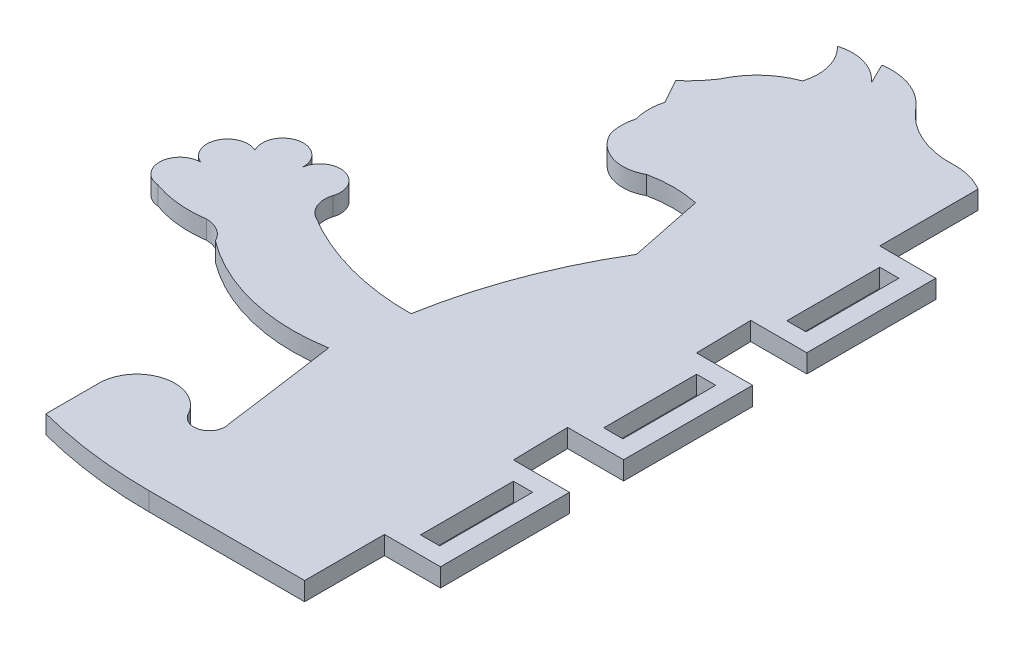
SolidWorks part; units mm, degrees
material "Roble"
ref_plane "Alzado" through (0, 0, 0) normal (0, 0, 1) x (1, 0, 0)
ref_plane "Planta" through (0, 0, 0) normal (0, 1, 0) x (1, 0, 0)
ref_plane "Vista lateral" through (0, 0, 0) normal (1, 0, 0) x (0, 0, -1)
sketch "Croquis1" plane through (0, 0, 0) normal (0, 1, 0) x (1, 0, 0)
  line L0 (0, 0) -> (-25.3533, 0)
  line L5 (0, 0) -> (0, 13)
  line L6 (0, 13) -> (9.123, 13)
  line L7 (9.123, 13) -> (9.123, 34)
  line L8 (9.123, 34) -> (0, 34)
  line L15 (-44.5719, 2.4618) -> (-44.5719, 11.0757)
  line L19 (0, 0) -> (-25.3533, 0) construction
  line L26 (-25.3533, 0) -> (-16.7689, 0) construction
  line L34 (8.9413, 42.9994) -> (8.9413, 63.9994)
  line L35 (3, 31) -> (6.123, 31)
  line L36 (-25.6818, 119.6671) -> (-24.0328, 116.2914)
  line L37 (-40.264, 100.6899) -> (-38.1037, 96.7778)
  line L38 (-21.4395, 85.0859) -> (-18.9699, 72.9989)
  line L39 (3, 31) -> (3, 15.877)
  line L40 (3, 15.877) -> (6.123, 15.877)
  line L41 (6.123, 31) -> (6.123, 15.877)
  line L42 (3, 31) -> (6.123, 15.877) construction
  line L43 (3, 15.877) -> (6.123, 31) construction
  line L44 (8.9413, 63.9994) -> (-0.1817, 63.9994)
  line L45 (-0.1817, 42.9994) -> (8.9413, 42.9994)
  line L46 (2.8183, 60.9994) -> (2.8183, 45.8764)
  line L47 (2.8183, 60.9994) -> (5.9413, 60.9994)
  line L48 (5.9413, 60.9994) -> (5.9413, 45.8764)
  line L49 (2.8183, 45.8764) -> (5.9413, 45.8764)
  line L50 (8.7596, 72.9989) -> (8.7596, 93.9989)
  line L51 (8.7596, 93.9989) -> (-0.3634, 93.9989)
  line L52 (-0.3634, 72.9989) -> (8.7596, 72.9989)
  line L53 (2.6366, 90.9989) -> (2.6366, 75.8759)
  line L54 (2.6366, 90.9989) -> (5.7596, 90.9989)
  line L55 (5.7596, 90.9989) -> (5.7596, 75.8759)
  line L56 (2.6366, 75.8759) -> (5.7596, 75.8759)
  line L57 (9.123, 13) -> (8.9413, 42.9994) construction
  line L58 (-0.3634, 109.9994) -> (-0.3634, 93.9989)
  line L59 (-0.3634, 72.9989) -> (-0.1817, 63.9994)
  line L60 (-0.1817, 42.9994) -> (0, 34)
  arc A2 (-25.3533, 0) -> (-44.5719, 2.4618) centre (-25.3533, 76.2491) cw
  arc A3 (-44.5719, 11.0757) -> (-32.9334, 13.9752) centre (-38.3915, 11.0757) cw
  arc A4 (-32.9334, 13.9752) -> (-28.2567, 15.984) centre (-30.6782, 15.1732) ccw
  arc A5 (-28.9551, 46.286) -> (-18.9699, 72.9989) centre (47.518, 32.9231) cw
  arc A27 (-30.842, 34.7581) -> (-55.1467, 40.6135) centre (-36.2361, 65.7381) cw
  arc A28 (-50.2849, 52.1173) -> (-28.9551, 46.286) centre (-29.4427, 86.4288) ccw
  arc A29 (-51.9646, 56.621) -> (-58.4575, 58.103) centre (-55.1467, 57.6438) ccw
  arc A30 (-67.7564, 43.8456) -> (-67.4325, 50.5189) centre (-67.483, 47.1768) cw
  arc A31 (-67.4325, 50.5189) -> (-64.712, 56.621) centre (-66.1758, 53.6162) cw
  arc A32 (-64.712, 56.621) -> (-58.4575, 58.103) centre (-61.7965, 58.2557) cw
  arc A33 (-51.9646, 56.621) -> (-50.2849, 52.1173) centre (-48.2704, 55.4337) ccw
  arc A34 (-55.1467, 40.6135) -> (-58.9366, 42.9798) centre (-58.9347, 38.7649) ccw
  arc A35 (-58.9366, 42.9798) -> (-67.7564, 43.8456) centre (-61.6014, 61.1914) cw
  arc A36 (-0.3634, 109.9994) -> (-5.9395, 111.4615) centre (-5.4975, 101.7837) ccw
  arc A37 (-5.9395, 111.4615) -> (-16.7855, 116.2914) centre (-6.544, 124.6968) cw
  arc A38 (-16.7855, 116.2914) -> (-25.6818, 119.6671) centre (-24.1754, 110.2264) ccw
  arc A39 (-24.0328, 116.2914) -> (-31.9625, 118.7107) centre (-29.8216, 111.5227) ccw
  arc A40 (-31.9625, 118.7107) -> (-29.9112, 110.9746) centre (-37.1875, 113.1852) cw
  arc A41 (-29.9112, 110.9746) -> (-36.9441, 104.4726) centre (-25.7031, 99.3683) ccw
  arc A42 (-36.9441, 104.4726) -> (-40.264, 100.6899) centre (-54.5544, 116.5804) cw
  arc A43 (-38.1037, 96.7778) -> (-38.1037, 92.0668) centre (-29.5649, 94.4223) ccw
  arc A44 (-38.1037, 92.0668) -> (-38.1037, 87.8794) centre (-30.5973, 89.9731) ccw
  arc A45 (-38.1037, 87.8794) -> (-29.4427, 85.0859) centre (-32.4832, 90.4822) ccw
  arc A46 (-29.4427, 85.0859) -> (-21.4395, 85.0859) centre (-25.4411, 66.3945) cw
  arc A47 (-30.842, 34.7581) -> (-28.2567, 15.984) centre (-1777.6791, -215.3558) cw
  point P12 (-23.4733, 84.4652)
  point P85 (-29.4427, 85.0859)
  point P86 (-12.3325, 83.3646)
  point P87 (-19.9931, 73.0595)
  point P88 (-19.9931, 85.0859)
  point P89 (-9.1966, 111.2905)
  point P90 (-8.0459, 111.2905)
  point P91 (-0.3634, 109.8003)
  point P92 (-7.9351, 111.16)
  point P93 (-16.7689, 115.9287)
  point P94 (-18.9699, 72.9989)
  point P95 (-21.4395, 85.0859)
  point P96 (0, 0)
  point P97 (-0.3634, 110.2264)
extrude "Saliente-Extruir1" add sketch "Croquis1" along normal blind 3
equation "\"mdf_wid\"= 3mm"
equation "\"mdf_hei\"= 15mm"
equation "\"alturagato\"= 110mm"
equation "\"D1@Croquis1\"=\"alturagato\""
equation "\"D2@Croquis1\"=\"mdf_hei\"+6"
equation "\"D3@Croquis1\"=\"mdf_wid\"*3+0.123"
equation "\"D4@Croquis1\"=\"mdf_wid\""
equation "\"D5@Croquis1\"=\"mdf_wid\"+0.123"
equation "\"D6@Croquis1\"=\"mdf_hei\"+0.123"
equation "\"D7@Croquis1\"=\"mdf_wid\""
equation "\"separacion\"= 13mm"
equation "\"D8@Croquis1\"=\"separacion\""
equation "\"sep2\"= 9mm"
